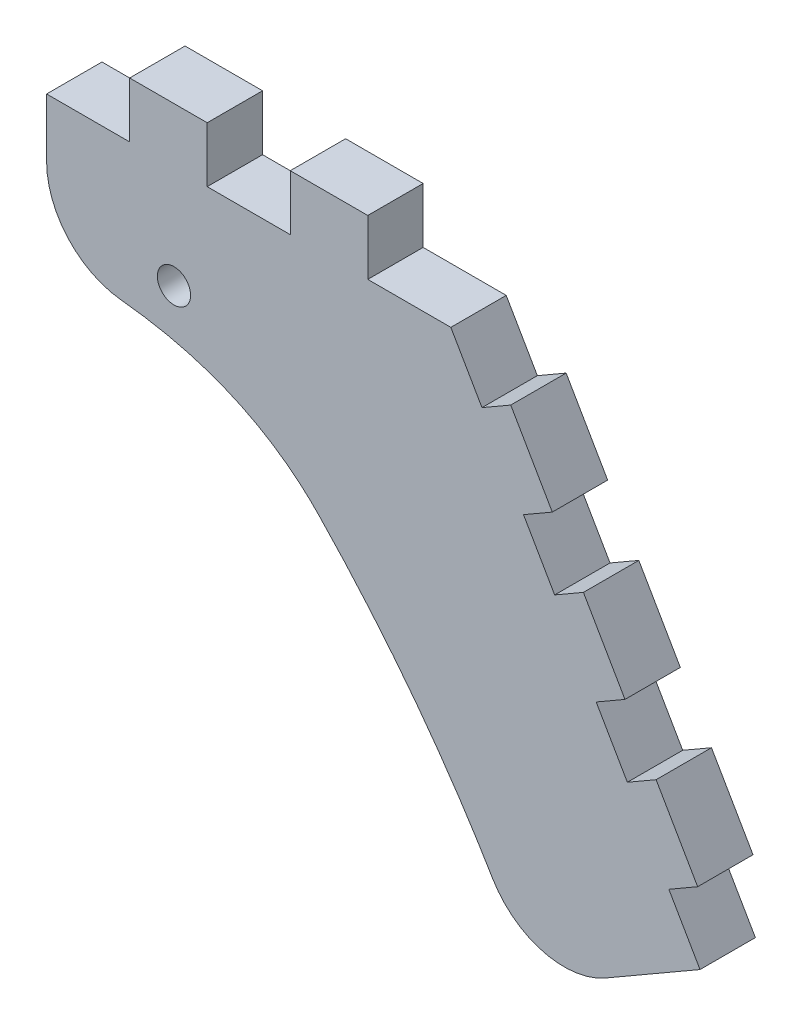
SolidWorks part; units mm, degrees
ref_plane "Front Plane" through (0, 0, 0) normal (0, 0, 1) x (1, 0, 0)
ref_plane "Top Plane" through (0, 0, 0) normal (0, 1, 0) x (1, 0, 0)
ref_plane "Right Plane" through (0, 0, 0) normal (1, 0, 0) x (0, 0, -1)
sketch "Sketch1" plane through (0, 0, 0) normal (0, 0, 1) x (1, 0, 0)
  line L0 (0, 0) -> (15, 0)
  line L1 (15, 0) -> (15, 10)
  line L2 (15, 10) -> (29, 10)
  line L3 (29, 10) -> (29, 0)
  line L4 (29, 0) -> (44, 0)
  line L5 (44, 0) -> (44, 10)
  line L6 (44, 10) -> (58, 10)
  line L7 (58, 10) -> (58, 0)
  line L8 (58, 0) -> (73, 0)
  line L9 (73, 0) -> (78.625, -9.7428)
  line L10 (78.625, -9.7428) -> (83.8212, -6.7428)
  line L11 (83.8212, -6.7428) -> (91.3212, -19.7332)
  line L12 (91.3212, -19.7332) -> (86.125, -22.7332)
  line L13 (86.125, -22.7332) -> (91.75, -32.476)
  line L14 (91.75, -32.476) -> (96.9462, -29.476)
  line L15 (96.9462, -29.476) -> (104.4462, -42.4663)
  line L16 (104.4462, -42.4663) -> (99.25, -45.4663)
  line L17 (99.25, -45.4663) -> (104.875, -55.2091)
  line L18 (104.875, -55.2091) -> (110.0712, -52.2091)
  line L19 (110.0712, -52.2091) -> (117.5712, -65.1995)
  line L20 (117.5712, -65.1995) -> (112.375, -68.1995)
  line L21 (112.375, -68.1995) -> (118, -77.9423)
  line L22 (118, -77.9423) -> (87.6891, -95.4423)
  line L23 (0, 0) -> (0, -25)
  line L24 (73, 0) -> (49.1605, -41.2913) construction
  line L25 (0, -21.5) -> (23, -21.5) construction
  circle A0 centre (23, -18.5) radius 3
  spline S0 degree 3 poles (0, -25) (17.2425, -24.6396) (35.9, -27.5043) (49.1605, -41.2913) knots 0 0 0 0 1 1 1 1
  spline S1 degree 3 poles (87.6891, -95.4423) (77.6602, -75.62) (64.8173, -57.5697) (49.1605, -41.2913) knots 0 0 0 0 1 1 1 1
  dimension "D1" = 120
  dimension "D12" = 23
  dimension "D13" = 6
  dimension "D14" = 3.5
  dimension "D2" = 15
  dimension "D3" = 14
  dimension "D4" = 11.25
  dimension "D5" = 10
  dimension "D6" = 15
  dimension "D7" = 6
  dimension "D8" = 25
  dimension "D9" = 35
  dimension "D10" = 60
  dimension "D11" = 47.679
extrude "Boss-Extrude1" add sketch "Sketch1" along normal blind 10
fillet "Fillet1" radius 15 2 edges at (87.6891, -95.4423, 5) (0, -25, 5)
